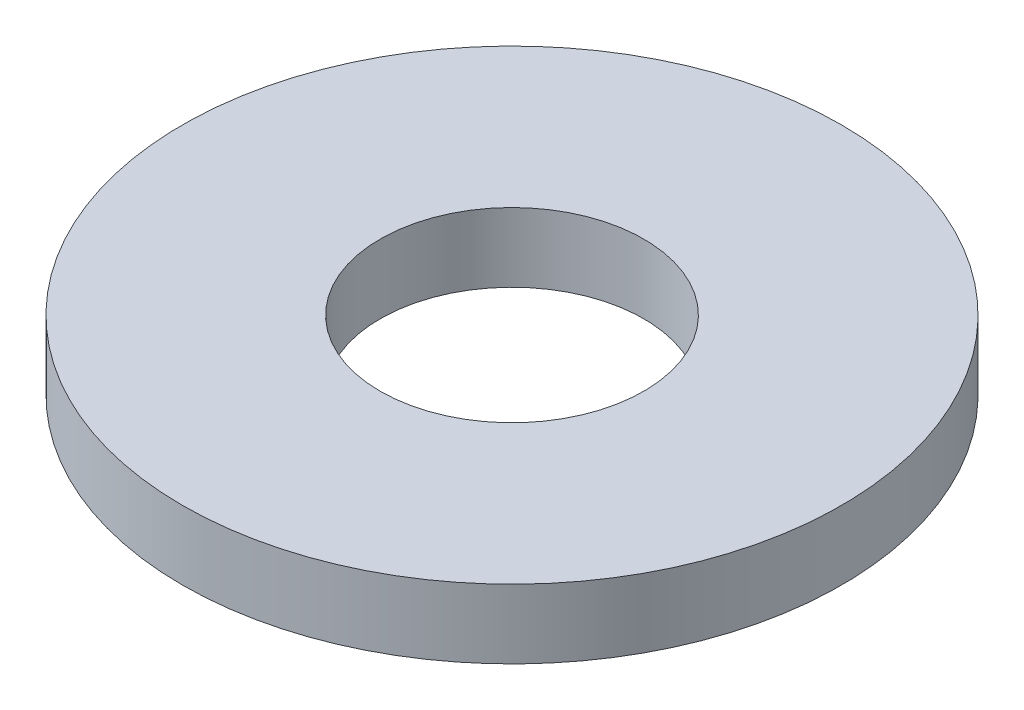
SolidWorks part; units mm, degrees
ref_plane "Front Plane" through (0, 0, 0) normal (0, 0, 1) x (1, 0, 0)
ref_plane "Top Plane" through (0, 0, 0) normal (0, 1, 0) x (1, 0, 0)
ref_plane "Right Plane" through (0, 0, 0) normal (1, 0, 0) x (0, 0, -1)
sketch "Sketch1" plane through (0, 0, 0) normal (0, 1, 0) x (1, 0, 0)
  circle A0 centre (0, 0) radius 4.0005
  dimension "OD" = 8.001
extrude "Boss-Extrude1" add sketch "Sketch1" along normal blind 0.8382
sketch "Sketch5" plane through (0, 0.8382, 0) normal (0, 1, 0) x (-1, 0, 0)
  circle A0 centre (0, 0) radius 1.6002
  dimension "ID" = 3.2004
extrude "Cut-Extrude1" cut sketch "Sketch5" against normal through all
